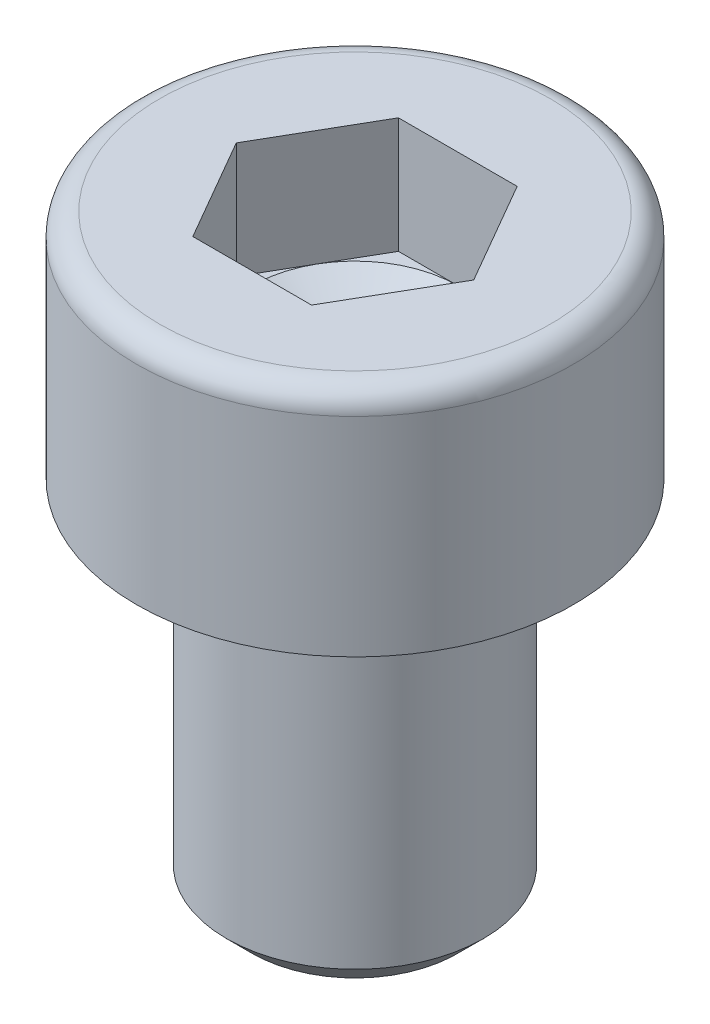
SolidWorks part; units mm, degrees
ref_plane "Plan1" through (0, 0, 0) normal (0, 0, 1) x (1, 0, 0)
ref_plane "Plan2" through (0, 0, 0) normal (0, 1, 0) x (1, 0, 0)
ref_plane "Plan3" through (0, 0, 0) normal (1, 0, 0) x (0, 0, -1)
sketch "Esquisse2" plane through (0, 0, 0) normal (0, 1, 0) x (1, 0, 0)
  circle A0 centre (0, 0) radius 2.5
  dimension "Diamètre nominal" = 5
extrude "Base-Extrusion" add sketch "Esquisse2" against normal blind 7
chamfer "Chanfrein1" distance 0.5 angle 45 1 edges at (0, -7, 2.5)
sketch "Esquisse5" plane through (0, 0, 0) normal (0, 0, 1) x (1, 0, 0)
  line L0 (-5.75, 0) -> (2.75, 0) construction
  line L1 (2, 4.5) -> (2, 2.25)
  line L2 (0, 0) -> (4.25, 0)
  line L3 (0, 0) -> (0, 1.0953)
  line L4 (2, 4.5) -> (3.8, 4.5)
  line L5 (4.25, 0) -> (4.25, 4.05)
  line L6 (2, 2.25) -> (0, 1.0953)
  line L7 (0, 4.5) -> (0, -7) construction
  line L8 (0, -6.5) -> (0, 0) construction
  line L9 (-2, -7) -> (2, -7) construction
  line L10 (2, 0) -> (-2, 0) construction
  arc A0 (4.25, 4.05) -> (3.8, 4.5) centre (3.8, 4.05) ccw
  dimension "D2" = 0.45
  dimension "D1" = 4.25
  dimension "Cote sur plats" = 4
  dimension "D3" = 60
  dimension "D4" = 2.25
  dimension "Diamètre tête" = 8.5
  dimension "Diamètre nominal" = 4.5
  dimension "D5" = 2
revolve "Boss.-Révol.1" add sketch "Esquisse5" angle 360 about L7
sketch "Esquisse7" plane through (0, 4.5, 0) normal (0, 1, 0) x (-1, 0, 0)
  line L0 (0, -2) -> (0, 2) construction
  line L1 (0, 0) -> (-1.1547, 2) construction
  line L2 (0, 0) -> (-1.7321, 1) construction
  line L3 (0, 0) -> (-2.3094, 0) construction
  line L4 (1.1547, 2) -> (-1.1547, 2)
  line L5 (-1.1547, 2) -> (-2.3094, 0)
  line L6 (1.1547, -2) -> (-1.1547, -2)
  line L7 (-1.1547, -2) -> (-2.3094, 0)
  line L8 (1.1547, 2) -> (2.3094, 0)
  line L9 (1.1547, -2) -> (2.3094, 0)
  circle A2 centre (0, 0) radius 2 construction
  dimension "D1" = 30
  dimension "D2" = 30
extrude "Enlèv. mat.-Extru.1" cut sketch "Esquisse7" against normal blind 2.25
equation "\"D1@Chanfrein1\" = \"Diamètre nominal@Esquisse2\"*0.1"
equation "\"D1@Esquisse5\" = \"Diamètre tête@Esquisse5\"/2"
equation "\"D2@Esquisse5\" = \"Diamètre nominal@Esquisse5\"*0.1"
equation "\"D4@Esquisse5\" = \"Diamètre nominal@Esquisse5\"/2"
equation "\"D5@Esquisse5\" = \"Cote sur plats@Esquisse5\"/2"
equation "\"D1@Enlèv. mat.-Extru.1\" = \"Diamètre nominal@Esquisse5\"/2"
